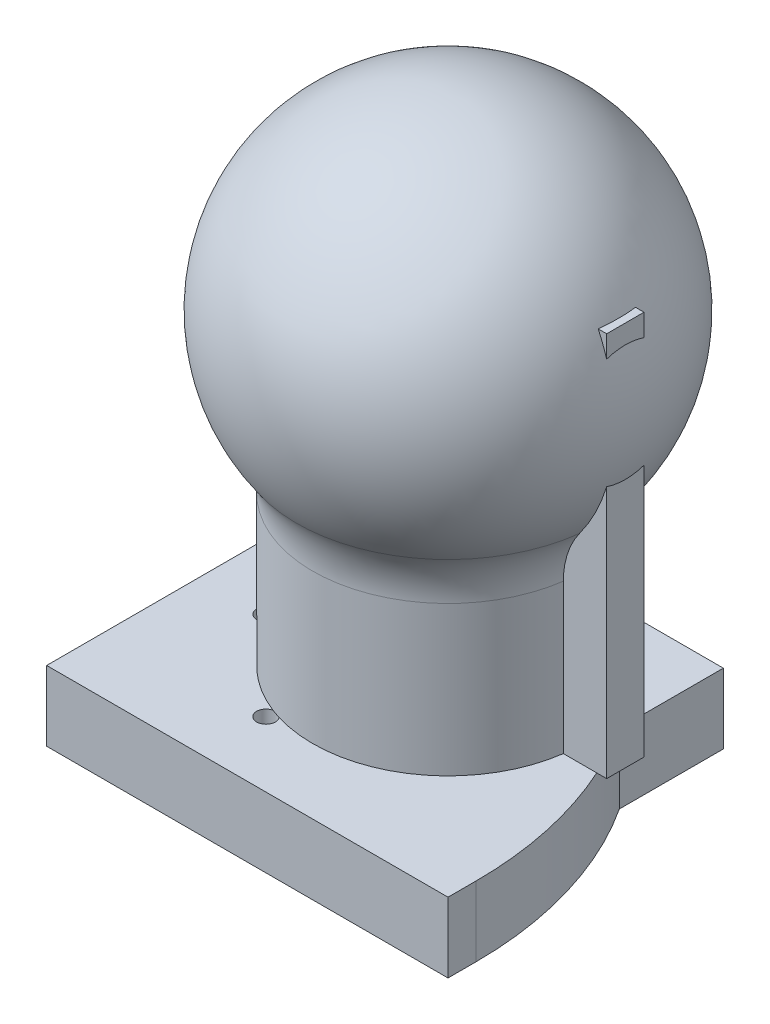
SolidWorks part; units mm, degrees
other "Markup1"
sketch "Sketch4" plane through (-40, 0, 40) normal (0, 0, 1) x (1, 0, 0)
ref_plane "Front Plane" through (0, 0, 0) normal (0, 0, 1) x (1, 0, 0)
ref_plane "Top Plane" through (0, 0, 0) normal (0, 1, 0) x (1, 0, 0)
ref_plane "Right Plane" through (0, 0, 0) normal (1, 0, 0) x (0, 0, -1)
sketch "Sketch1" plane through (0, 0, 0) normal (0, 1, 0) x (1, 0, 0)
  circle A0 centre (0, 0) radius 29
  dimension "D1" = 58
extrude "Boss-Extrude1" add sketch "Sketch1" along normal blind 32
sketch "Sketch2" plane through (0, 0, 0) normal (0, 0, 1) x (1, 0, 0)
  line L0 (0, 0) -> (0, 66) construction
  line L1 (-29, 32) -> (-29, 0) construction
  line L2 (29, 32) -> (-29, 32) construction
  line L3 (0, 66) -> (0, 106) construction
  line L4 (-29, 32) -> (0, 32)
  line L5 (0, 32) -> (0, 106)
  arc A0 (0, 106) -> (-32.4197, 42.5701) centre (0, 66) ccw
  arc A1 (-32.4197, 42.5701) -> (-29, 32) centre (-47.0455, 32) cw
  dimension "D1" = 80
  dimension "D2" = 34
revolve "Revolve1" add sketch "Sketch2" angle 360 about L5
sketch "Sketch3" plane through (0, 0, 0) normal (1, 0, 0) x (0, 0, -1)
  line L0 (0, 106) -> (0, 0) construction
  line L1 (-29, 0) -> (29, 0) construction
  line L2 (4, 0) -> (-4, 0)
  line L3 (4, 0) -> (4, 82.55)
  line L4 (4, 82.55) -> (-4, 82.55)
  line L5 (-4, 0) -> (-4, 82.55)
  arc A0 (32.4197, 42.5701) -> (-32.4197, 42.5701) centre (0, 66) ccw construction
  point P12 (0, 82.55)
  dimension "D1" = 82.55
  dimension "D2" = 8
extrude "Boss-Extrude2" add sketch "Sketch3" along normal blind 38
sketch "Sketch5" plane through (0, 0, 0) normal (1, 0, 0) x (0, 0, -1)
  line L0 (29, 0) -> (29, 32) construction
  line L1 (-29, 0) -> (29, 0)
  line L2 (-29, 0) -> (-29, -15)
  line L3 (-29, -15) -> (29, -15)
  line L4 (29, 0) -> (29, -15)
  dimension "D1" = 15
extrude "Boss-Extrude3" add sketch "Sketch5" along normal mid plane 60
sketch "Sketch6" plane through (0, -15, 0) normal (0, -1, 0) x (1, 0, 0)
  line L0 (0, 29) -> (0, -29) construction
  line L1 (-37, -43) -> (-43, -43)
  line L2 (43, 37) -> (43, 43)
  line L3 (43, 43) -> (-43, 43)
  line L4 (-43, -43) -> (-43, 43)
  line L5 (30, 29) -> (-30, 29) construction
  line L6 (30, -29) -> (-30, -29) construction
  arc A1 (-37, -43) -> (43, 37) centre (-37, 37) ccw
  point P4 (-43, 0)
  dimension "D2" = 80
  dimension "D1" = 86
extrude "Boss-Extrude4" add sketch "Sketch6" against normal up to surface (15 mm away) up to face at (-22.25, 0, 0)
sketch "Sketch7" plane through (0, 0, 0) normal (0, 1, 0) x (1, 0, 0)
  line L0 (-43, 43) -> (-43, -43) construction
  line L1 (-37, 43) -> (-43, 43) construction
  line L2 (-43, -43) -> (29, 29) construction
  line L3 (30, 29) -> (8.2106, 29) construction
  circle A0 centre (-29, -10) radius 2
  circle A1 centre (-10, -29) radius 2
  point P4 (25.4691, 26.0448)
  point P9 (-43, -43)
  point P11 (29.0377, 29)
  dimension "D2" = 4
  dimension "D1" = 14
  dimension "D3" = 53
  dimension "D4" = 45
extrude "Cut-Extrude2" cut sketch "Sketch7" against normal through all
